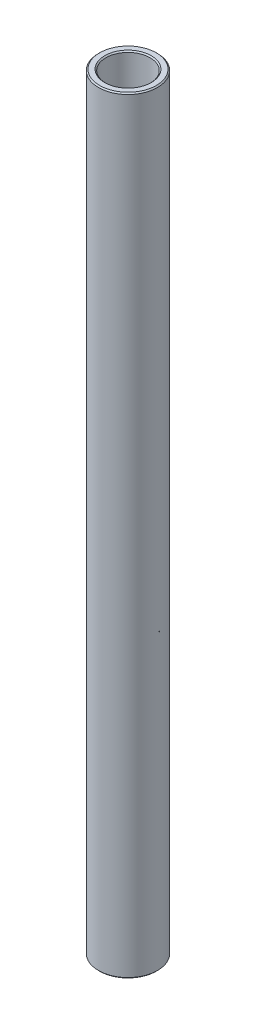
SolidWorks part; units mm, degrees
ref_plane "Front Plane" through (0, 0, 0) normal (0, 0, 1) x (1, 0, 0)
ref_plane "Top Plane" through (0, 0, 0) normal (0, 1, 0) x (1, 0, 0)
ref_plane "Right Plane" through (0, 0, 0) normal (1, 0, 0) x (0, 0, -1)
sketch "Sketch1" plane through (0, 0, 0) normal (0, 0, 1) x (1, 0, 0)
  line L0 (0, 11.6086) -> (0, -11.6086) construction
  line L1 (4.7625, 82.55) -> (6.35, 82.55)
  line L2 (6.35, 82.55) -> (6.35, -82.55)
  line L3 (6.35, -82.55) -> (4.7625, -82.55)
  line L4 (4.7625, -82.55) -> (4.7625, 82.55)
  line L5 (4.7625, 0) -> (0, 0) construction
  dimension "D1" = 9.525
  dimension "D2" = 12.7
  dimension "D3" = 165.1
revolve "Revolve1" add sketch "Sketch1" angle 360 about L0
chamfer "Chamfer1" distance 0.254 angle 45 4 edges at (-4.7625, -82.55, 0) (-6.35, -82.55, 0) (-6.35, 82.55, 0) (-4.7625, 82.55, 0)
